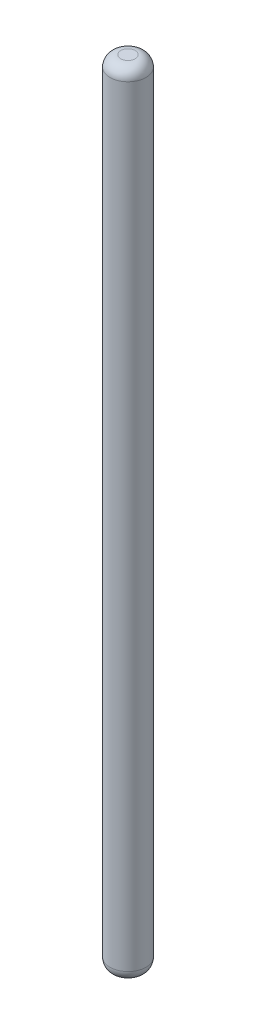
SolidWorks part; units mm, degrees
ref_plane "Front Plane" through (0, 0, 0) normal (0, 0, 1) x (1, 0, 0)
ref_plane "Top Plane" through (0, 0, 0) normal (0, 1, 0) x (1, 0, 0)
ref_plane "Right Plane" through (0, 0, 0) normal (1, 0, 0) x (0, 0, -1)
sketch "Sketch1" plane through (0, 0, 0) normal (0, 1, 0) x (1, 0, 0)
  circle A0 centre (0, 0) radius 2.5
  dimension "D1" = 5
extrude "Boss-Extrude1" add sketch "Sketch1" along normal blind 110
fillet "Fillet1" radius 1.5 2 edges at (0, 0, 2.5) (0, 110, 2.5)
